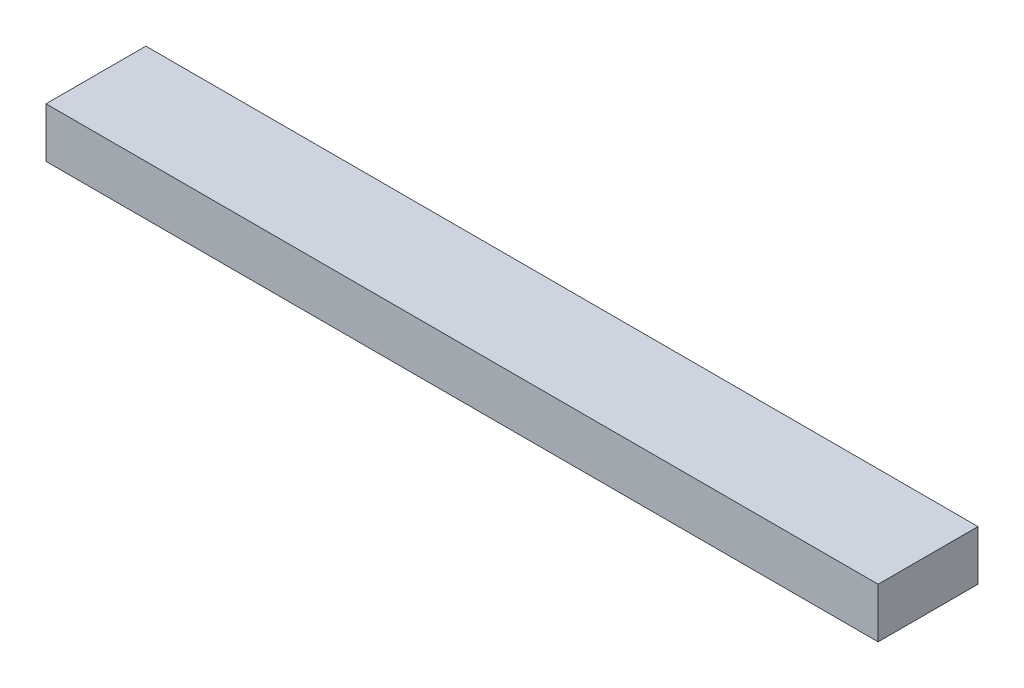
SolidWorks part; units mm, degrees
material "3.1355 (EN-AW 2024)"
ref_plane "Спереди" through (0, 0, 0) normal (0, 0, 1) x (1, 0, 0)
ref_plane "Сверху" through (0, 0, 0) normal (0, 1, 0) x (1, 0, 0)
ref_plane "Справа" through (0, 0, 0) normal (1, 0, 0) x (0, 0, -1)
sketch "Эскиз1" plane through (0, 0, 0) normal (0, 1, 0) x (1, 0, 0)
  line L0 (0, 0) -> (0, 30)
  line L1 (0, 30) -> (250, 30)
  line L2 (250, 30) -> (250, 0)
  line L3 (250, 0) -> (0, 0)
  dimension "D1" = 30
  dimension "D2" = 250
extrude "Бобышка-Вытянуть1" add sketch "Эскиз1" along normal blind 15
